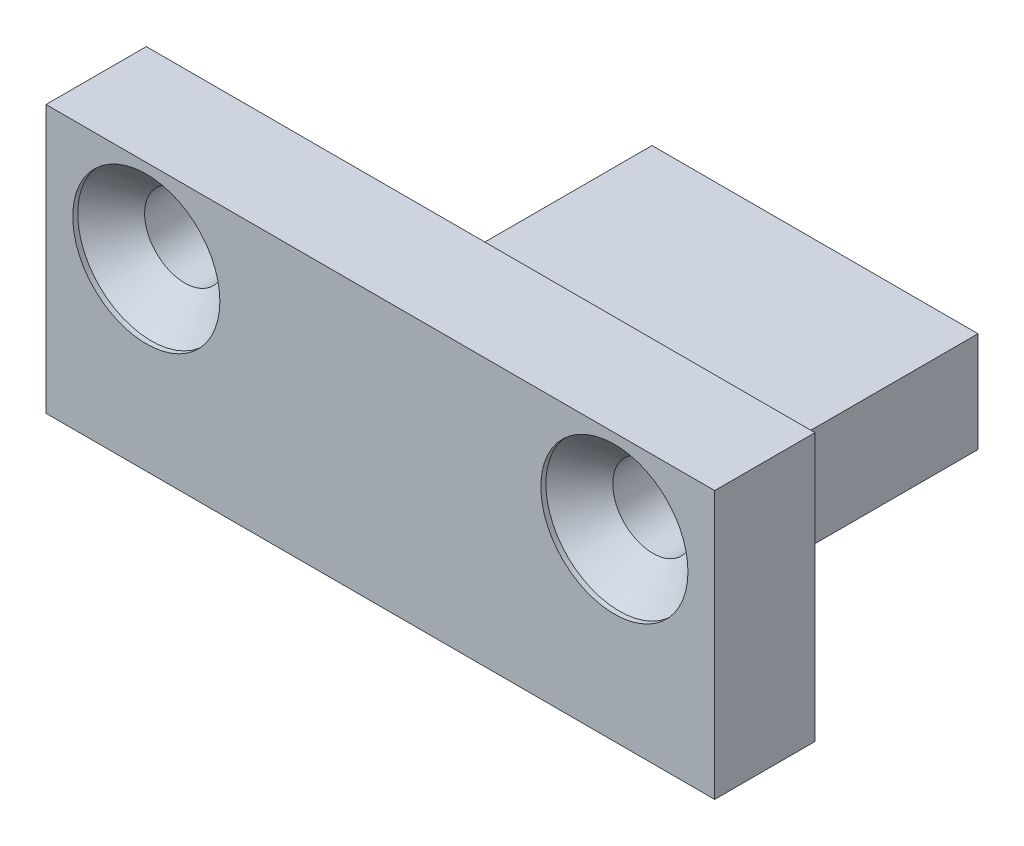
SolidWorks part; units mm, degrees
ref_plane "Front Plane" through (0, 0, 0) normal (0, 0, 1) x (1, 0, 0)
ref_plane "Top Plane" through (0, 0, 0) normal (0, 1, 0) x (1, 0, 0)
ref_plane "Right Plane" through (0, 0, 0) normal (1, 0, 0) x (0, 0, -1)
sketch "Sketch1" plane through (0, 0, 0) normal (1, 0, 0) x (0, 0, -1)
  line L0 (0, 0) -> (10, 0)
  line L1 (10, 0) -> (10, -3)
  line L2 (10, -3) -> (-3, -3)
  line L3 (-3, -3) -> (-3, 5)
  line L4 (-3, 5) -> (0, 5)
  line L5 (0, 5) -> (0, 0)
  dimension "D1" = 3
  dimension "D2" = 10
  dimension "D3" = 5
  dimension "D4" = 3
extrude "Boss-Extrude1" add sketch "Sketch1" along normal mid plane 20
sketch "Sketch2" plane through (0, 0, 0) normal (0, 1, 0) x (1, 0, 0)
  line L0 (10, 0) -> (-10, 0) construction
  line L1 (-10, 10) -> (-4.875, 10)
  line L2 (-10, 10) -> (-10, 0)
  line L3 (-10, 0) -> (-4.875, 0)
  line L4 (-4.875, 10) -> (-4.875, 0)
  line L6 (10, 10) -> (4.875, 10)
  line L7 (10, 10) -> (10, 0)
  line L8 (10, 0) -> (4.875, 0)
  line L9 (4.875, 10) -> (4.875, 0)
  dimension "D1" = 9.75
extrude "Cut-Extrude1" cut sketch "Sketch2" against normal through all
hole_wizard "CSK for M2 Flat Head Machine Screw1" positions "Sketch5" profile "Sketch4" countersink size "M2" standard "ANSI Metric"
sketch "Sketch5" plane through (0, 0, 3) normal (0, 0, 1) x (1, 0, 0)
  line L0 (-7, 2.5) -> (7, 2.5) construction
  line L3 (0, 2.5) -> (0, -3) construction
  line L4 (10, -3) -> (-10, -3) construction
  line L5 (10, 5) -> (-10, 5) construction
  point P0 (7, 2.5)
  point P2 (-7, 2.5)
  dimension "D1" = 14
  dimension "D2" = 2.5
sketch "Sketch4" plane through (7, 2.5, 3) normal (1, 0, 0) x (0, -1, 0)
  line L0 (0, 0) -> (0, 20.721)
  line L1 (0, 20.721) -> (1.2, 20)
  line L2 (1.2, 20) -> (1.2, 1.15)
  line L3 (1.2, 1.15) -> (2.2, 0.15)
  line L4 (2.2, 0.15) -> (2.2, 0)
  line L6 (2.2, 0) -> (0, 0)
  line L7 (-1.2, 1.15) -> (-2.2, 0.15) construction
  line L10 (0, 20.721) -> (-1.2, 20) construction
  line L11 (0, -6.35) -> (0, 107.95) construction
  dimension "Hole Dia." = 2.4
  dimension "Hole Depth" = 20
  dimension "C'Sink Dia." = 4.4
  dimension "C'Sink Angle" = 90
  dimension "Drill Angle" = 118
  dimension "Head Clearance" = 0.15
